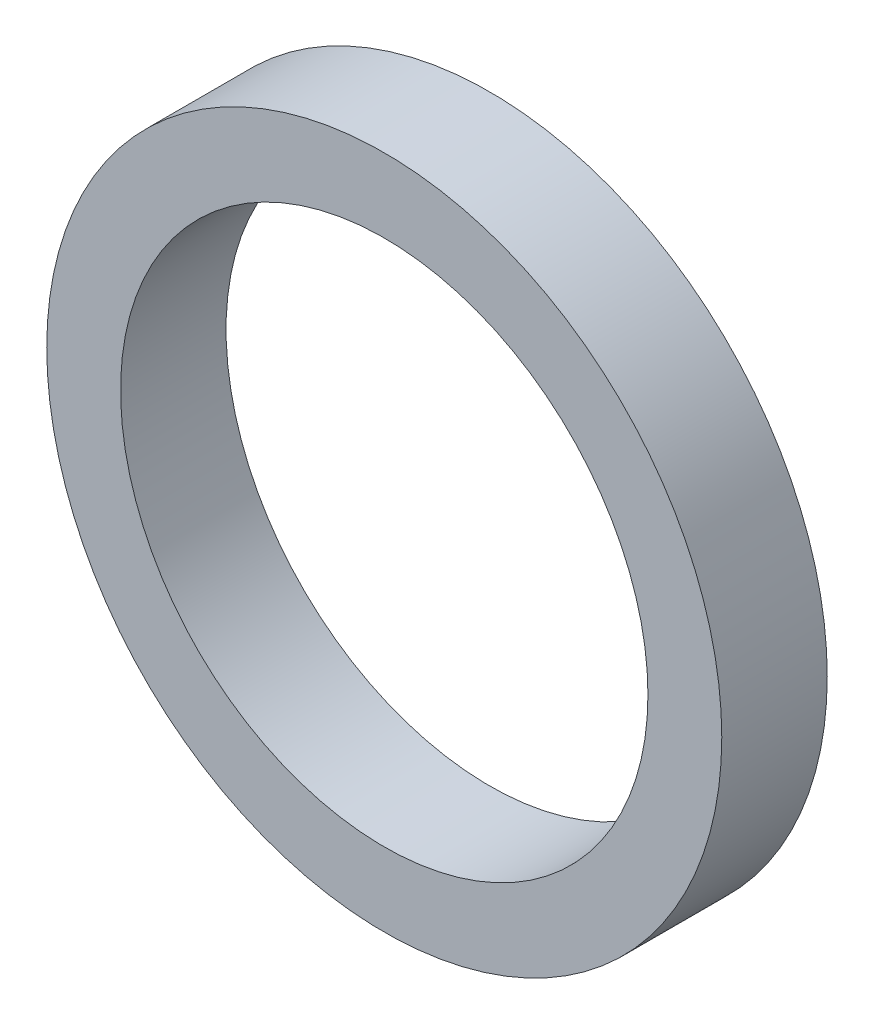
SolidWorks part; units mm, degrees
ref_plane "Front Plane" through (0, 0, 0) normal (0, 0, 1) x (1, 0, 0)
ref_plane "Top Plane" through (0, 0, 0) normal (0, 1, 0) x (1, 0, 0)
ref_plane "Right Plane" through (0, 0, 0) normal (1, 0, 0) x (0, 0, -1)
sketch "Sketch1" plane through (0, 0, 0) normal (0, 0, 1) x (1, 0, 0)
  circle A0 centre (0, 0) radius 25
  circle A1 centre (0, 0) radius 32
  dimension "D1" = 25
  dimension "D2" = 32
extrude "Boss-Extrude1" add sketch "Sketch1" along normal mid plane 10
